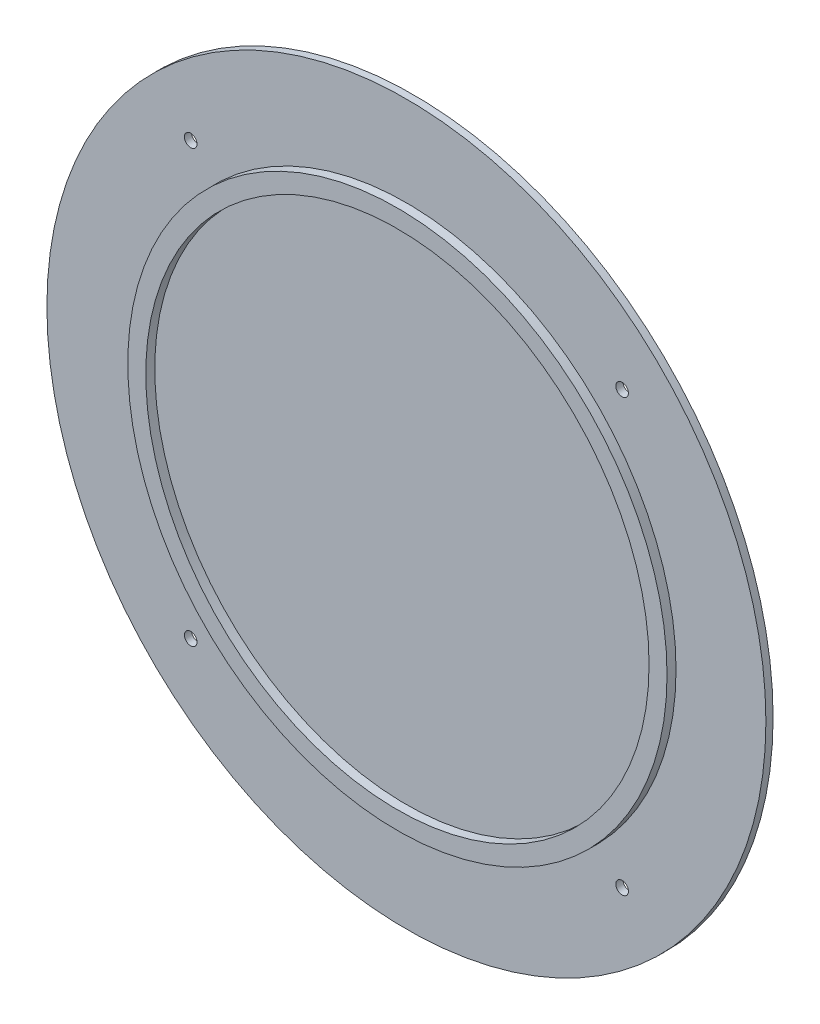
SolidWorks part; units mm, degrees
ref_plane "Alzado" through (0, 0, 0) normal (0, 0, 1) x (1, 0, 0)
ref_plane "Planta" through (0, 0, 0) normal (0, 1, 0) x (1, 0, 0)
ref_plane "Vista lateral" through (0, 0, 0) normal (1, 0, 0) x (0, 0, -1)
sketch "Croquis1" plane through (0, 0, 0) normal (0, 0, 1) x (1, 0, 0)
  circle A0 centre (0, 0) radius 20
  dimension "D1" = 40
extrude "Saliente-Extruir1" add sketch "Croquis1" along normal blind 0.4
sketch "Croquis3" plane through (0, 0, 0.4) normal (0, 0, 1) x (1, 0, 0)
  line L0 (0, 0) -> (0, 12) construction
  line L1 (0, 0) -> (12, 0) construction
  circle A0 centre (12, 12) radius 0.35
  circle A1 centre (-12, 12) radius 0.35
  circle A2 centre (12, -12) radius 0.35
  circle A3 centre (-12, -12) radius 0.35
  dimension "D3" = 0.7
  dimension "D1" = 12
  dimension "D2" = 12
extrude "Cortar-Extruir1" cut sketch "Croquis3" against normal blind 10
sketch "Croquis2" plane through (0, 0, 0.4) normal (0, 0, 1) x (1, 0, 0)
  circle A0 centre (0, 0) radius 14
  circle A1 centre (0, 0) radius 15
  dimension "D1" = 28
  dimension "D2" = 30
extrude "Saliente-Extruir2" add sketch "Croquis2" along normal blind 0.5
